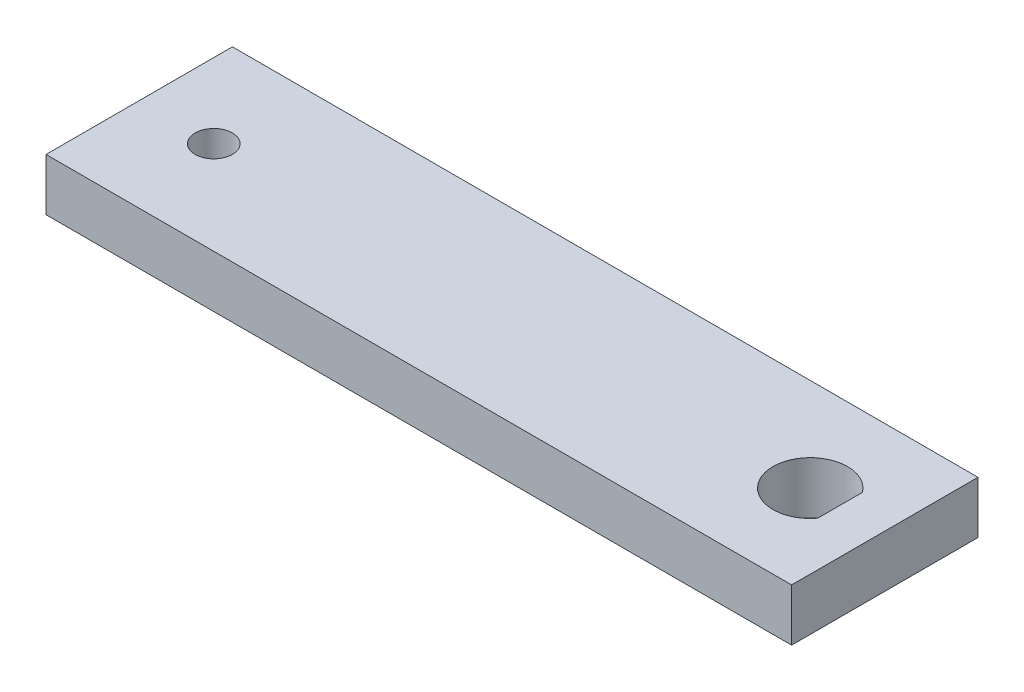
SolidWorks part; units mm, degrees
ref_plane "Front" through (0, 0, 0) normal (0, 0, 1) x (1, 0, 0)
ref_plane "Top" through (0, 0, 0) normal (0, 1, 0) x (-1, 0, 0)
ref_plane "Right" through (0, 0, 0) normal (1, 0, 0) x (0, 0, -1)
sketch "Sketch1" plane through (0, 0, 0) normal (0, 0, 1) x (1, 0, 0)
  line L0 (0, 0) -> (100, 0)
  line L1 (0, 0) -> (0, 7)
  line L2 (100, 7) -> (0, 7)
  line L3 (100, 7) -> (100, 0)
  dimension "D1" = 7
  dimension "D2" = 100
extrude "Base-Extrude" add sketch "Sketch1" along normal blind 25
sketch "Sketch2" plane through (0, 7, 0) normal (0, 1, 0) x (-1, 0, 0)
  line L0 (-100, 25) -> (-100, 0) construction
  line L1 (-100, 25) -> (0, 25) construction
  line L2 (-94, 9.5) -> (-94, 15.5)
  arc A0 (-94, 9.5) -> (-94, 15.5) centre (-90, 12.5) ccw
  dimension "D1" = 10
  dimension "D2" = 10
  dimension "D3" = 12.5
  dimension "D4" = 4
extrude "Cut-Extrude1" cut sketch "Sketch2" against normal through all
sketch "Sketch3" plane through (0, 7, 0) normal (0, 1, 0) x (-1, 0, 0)
  line L0 (0, 25) -> (0, 0) construction
  circle A0 centre (-10, 12.5) radius 2.5
  arc A1 (-94, 9.5) -> (-94, 15.5) centre (-90, 12.5) ccw construction
  point P5 (-90, 12.5)
  dimension "D1" = 5
  dimension "D2" = 10
extrude "Cut-Extrude2" cut sketch "Sketch3" against normal through all
